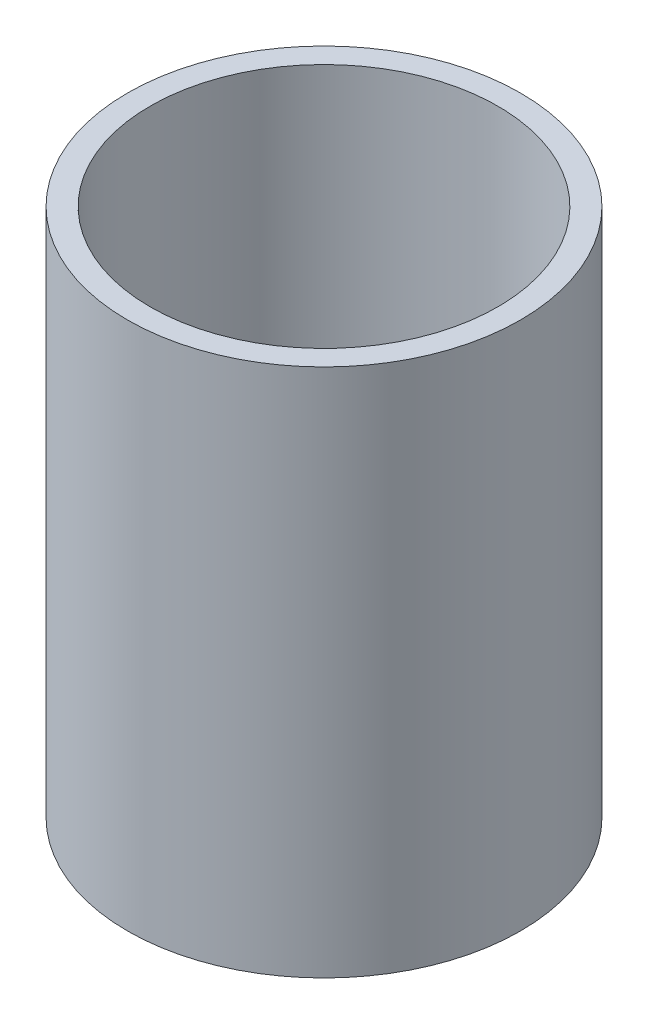
SolidWorks part; units mm, degrees
ref_plane "Front Plane" through (0, 0, 0) normal (0, 0, 1) x (1, 0, 0)
ref_plane "Top Plane" through (0, 0, 0) normal (0, 1, 0) x (1, 0, 0)
ref_plane "Right Plane" through (0, 0, 0) normal (1, 0, 0) x (0, 0, -1)
sketch "Sketch1" plane through (0, 0, 0) normal (0, 1, 0) x (1, 0, 0)
  circle A0 centre (0, 0) radius 26
  circle A1 centre (0, 0) radius 23
  dimension "D1" = 52
  dimension "D2" = 46
extrude "Boss-Extrude1" add sketch "Sketch1" along normal mid plane 70
